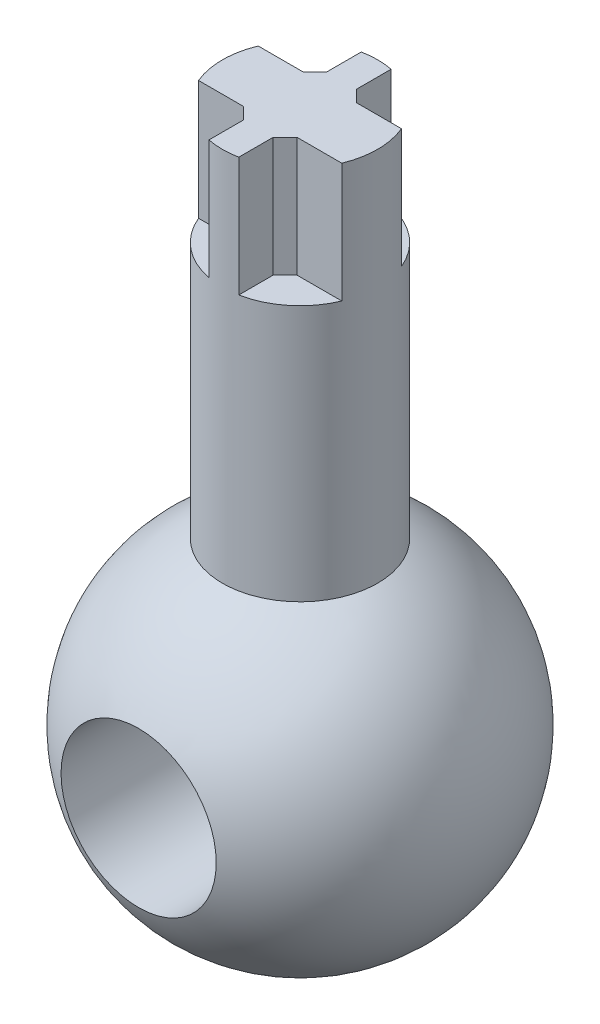
SolidWorks part; units mm, degrees
ref_plane "Plane1" through (0, 0, 0) normal (0, 0, 1) x (1, 0, 0)
ref_plane "Plane2" through (0, 0, 0) normal (0, 1, 0) x (1, 0, 0)
ref_plane "Plane3" through (0, 0, 0) normal (1, 0, 0) x (0, 0, -1)
other "Configuration Table"
sketch "s1" plane through (0, 0, 0) normal (0, 0, 1) x (1, 0, 0)
  line L0 (-56.6721, 0) -> (83.8972, 0) construction
  line L1 (-15, 0) -> (15, 0)
  arc A0 (15, 0) -> (-15, 0) centre (0, 0) ccw
  dimension "D1" = 15
revolve "1" add sketch "s1" angle 360 about L0
sketch "s2" plane through (0, 0, 0) normal (0, 1, 0) x (1, 0, 0)
  circle A0 centre (0, 0) radius 6.5
  dimension "D1" = 13
extrude "2" add sketch "s2" along normal blind 45
sketch "s3" plane through (0, 45, 0) normal (0, 1, 0) x (-1, 0, 0)
  line L0 (-10.6288, 0) -> (13.9677, 0) construction
  line L1 (56.6721, 0) -> (-83.8972, 0) construction
  line L2 (0, -10.8514) -> (0, 14.1903) construction
  line L3 (-1.25, -6.3787) -> (-1.25, -2.5)
  line L4 (1.25, -6.3787) -> (1.25, -2.5)
  line L5 (-6, 2.5) -> (-1.25, 2.5)
  line L6 (-6, -2.5) -> (-1.25, -2.5)
  line L7 (-1.25, 2.5) -> (-1.25, 6.3787)
  line L8 (1.25, 2.5) -> (1.25, 6.3787)
  line L9 (1.25, -2.5) -> (6, -2.5)
  line L10 (1.25, 2.5) -> (6, 2.5)
  circle A0 centre (0, 0) radius 6.5 construction
  arc A1 (-6, -2.5) -> (-1.25, -6.3787) centre (0, 0) ccw
  arc A2 (6, 2.5) -> (1.25, 6.3787) centre (0, 0) ccw
  arc A3 (-1.25, 6.3787) -> (-6, 2.5) centre (0, 0) ccw
  arc A4 (1.25, -6.3787) -> (6, -2.5) centre (0, 0) ccw
  dimension "D1" = 5
  dimension "D2" = 2.5
extrude "3" cut sketch "s3" against normal blind 10
chamfer "4" distance 1 angle 45 4 edges at (-1.25, 40, -2.5) (1.25, 40, -2.5) (1.25, 40, 2.5) (-1.25, 40, 2.5)
sketch "s5" plane through (0, 0, 0) normal (0, 0, 1) x (1, 0, 0)
  circle A0 centre (0, 0) radius 6.5
  dimension "D1" = 13
extrude "5" cut sketch "s5" against normal through all and the other way through all
fillet "Fillet1" [suppressed] radius 1.5
